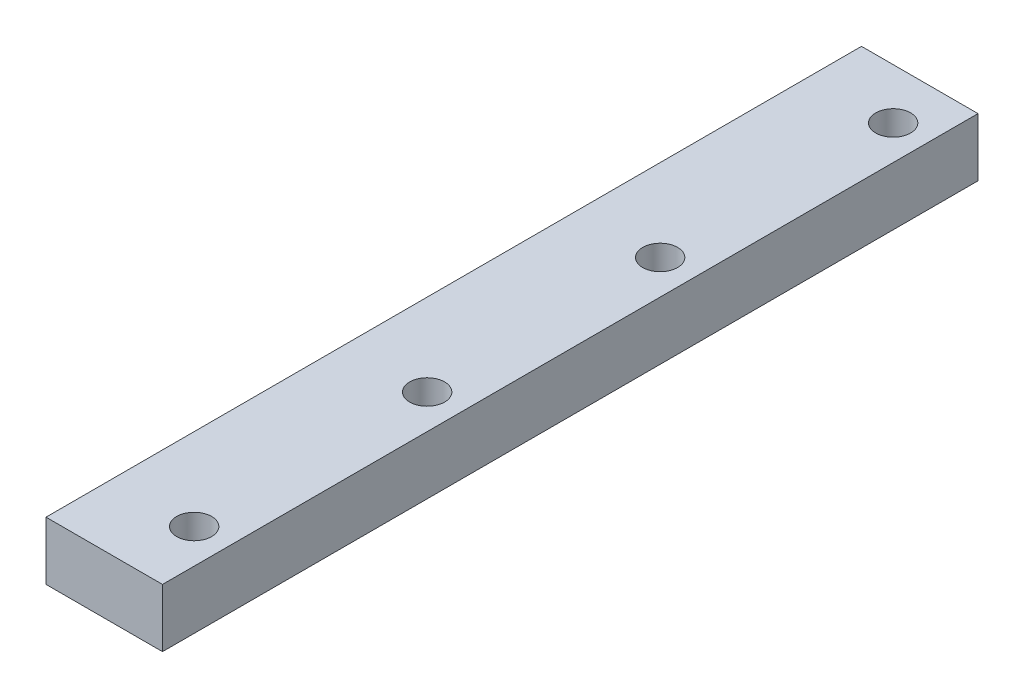
SolidWorks part; units mm, degrees
ref_plane "Front Plane" through (0, 0, 0) normal (0, 0, 1) x (1, 0, 0)
ref_plane "Top Plane" through (0, 0, 0) normal (0, 1, 0) x (1, 0, 0)
ref_plane "Right Plane" through (0, 0, 0) normal (1, 0, 0) x (0, 0, -1)
sketch "Sketch1" plane through (0, 0, 0) normal (0, 0, 1) x (1, 0, 0)
  line L0 (20, 20.188) -> (0, 20.188)
  line L1 (0, 20.188) -> (0, 10.188)
  line L5 (20, 10.188) -> (20, 20.188)
  line L6 (0, 10.188) -> (20, 10.188)
  dimension "D1" = 20
  dimension "D2" = 10
  dimension "D3" = 10
extrude "Boss-Extrude1" add sketch "Sketch1" along normal blind 140
sketch "Sketch2" plane through (0, 20.188, 0) normal (0, 1, 0) x (1, 0, 0)
  circle A0 centre (14.1086, -8.6737) radius 3
extrude "Cut-Extrude1" cut sketch "Sketch2" against normal blind 140
pattern_linear "LPattern1" count 4 spacing 40 along (0, 0, 1) of "Cut-Extrude1"
